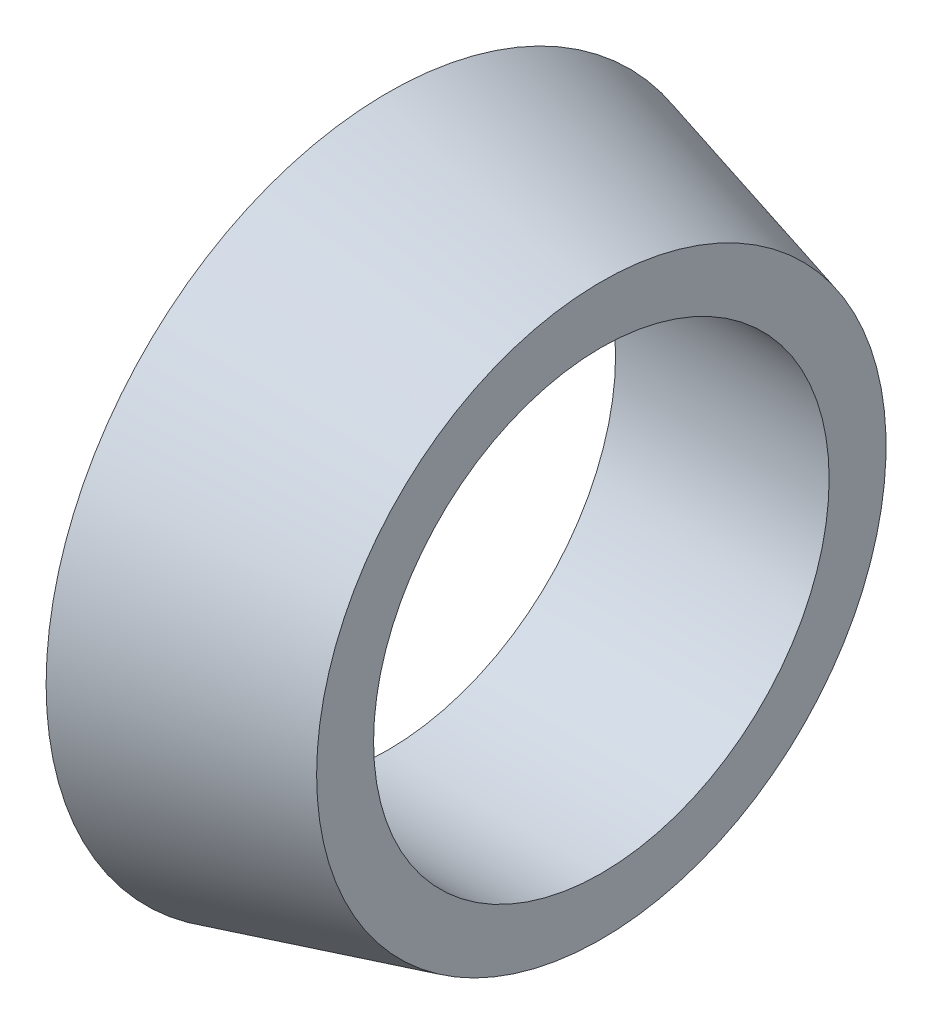
SolidWorks part; units mm, degrees
ref_plane "Płaszczyzna XY" through (0, 0, 0) normal (0, 0, 1) x (1, 0, 0)
ref_plane "Płaszczyzna XZ" through (0, 0, 0) normal (0, 1, 0) x (1, 0, 0)
ref_plane "Płaszczyzna YZ" through (0, 0, 0) normal (1, 0, 0) x (0, 0, -1)
sketch "Szkic1" plane through (0, 0, 0) normal (0, 0, 1) x (1, 0, 0)
  line L0 (0, 4) -> (0, 6)
  line L1 (0, 6) -> (3.75, 5)
  line L2 (3.75, 5) -> (3.75, 4)
  line L3 (3.75, 4) -> (0, 4)
  line L4 (0, 0) -> (22.8523, 0) construction
  dimension "D1" = 8
  dimension "D2" = 5
  dimension "D3" = 3.75
  dimension "D4" = 6
revolve "Obrót1" add sketch "Szkic1" angle 360 about L4
